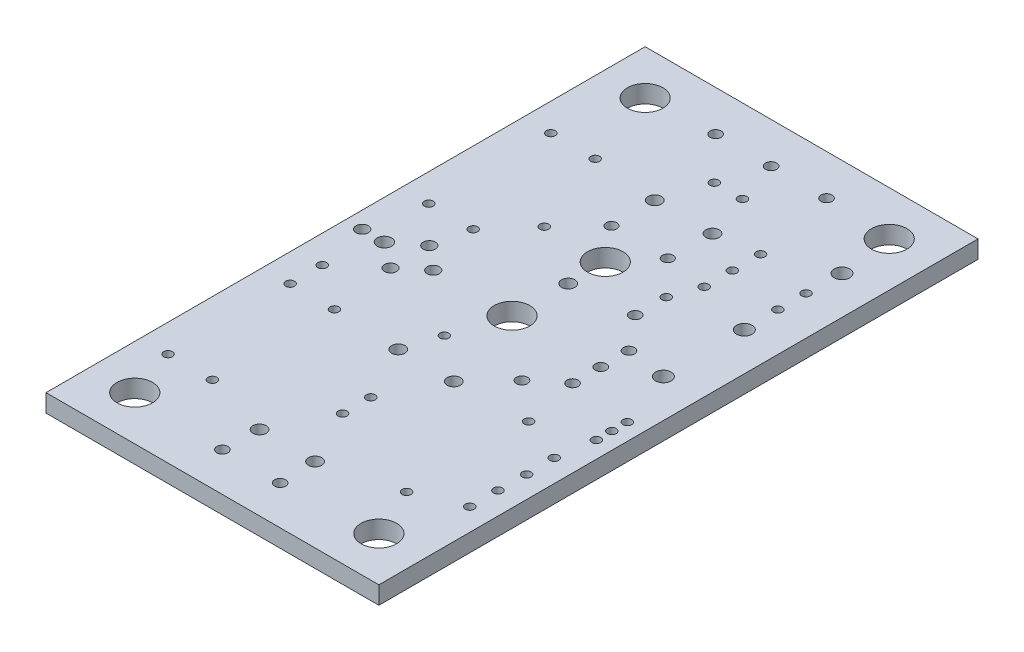
SolidWorks part; units mm, degrees
ref_plane "Plan de face" through (0, 0, 0) normal (0, 0, 1) x (1, 0, 0)
ref_plane "Plan de dessus" through (0, 0, 0) normal (0, 1, 0) x (1, 0, 0)
ref_plane "Plan de droite" through (0, 0, 0) normal (1, 0, 0) x (0, 0, -1)
sketch "Esquisse2" plane through (0, 0, 0) normal (0, 1, 0) x (1, 0, 0)
  line L0 (-3.7147, 54) -> (37.2981, 54) construction
  line L1 (0, 0) -> (30, 0)
  line L2 (0, 0) -> (0, 54)
  line L3 (0, 54) -> (30, 54)
  line L4 (30, 0) -> (30, 54)
  line L5 (30, 56.5565) -> (30, 31.4196) construction
  line L6 (21.4, 56.5565) -> (21.4, 32.6009) construction
  line L7 (39.5472, 43) -> (18.8423, 43) construction
  line L8 (22.2978, 35.4025) -> (8.7432, 35.4025) construction
  line L9 (9.5, 39.4589) -> (9.5, 30.7618) construction
  line L10 (0, 55.1911) -> (0, 37.1099) construction
  line L11 (20.5, 33.9139) -> (20.5, 38.4988) construction
  circle A0 centre (17.6225, 42.4459) radius 0.5994
  circle A1 centre (12.4206, 42.4459) radius 0.5994
  circle A2 centre (15.0216, 32.0446) radius 0.5994
  circle A3 centre (15.0038, 35.4025) radius 1.6002
  circle A4 centre (17.5997, 3.5001) radius 0.5004
  circle A5 centre (12.4003, 3.5001) radius 0.5004
  circle A6 centre (15.0012, 50.3504) radius 0.5004
  circle A7 centre (20, 50.3504) radius 0.5004
  circle A8 centre (10, 50.3504) radius 0.5004
  circle A9 centre (12.4993, 19.2507) radius 0.5994
  circle A10 centre (12.4993, 6.7488) radius 0.5994
  circle A11 centre (17.5006, 19.2507) radius 0.5994
  circle A12 centre (17.5006, 6.7488) radius 0.5994
  circle A13 centre (20.5003, 22.4003) radius 0.5004
  circle A14 centre (20.5003, 32.6009) radius 0.5004
  circle A15 centre (12.4612, 38.4988) radius 0.4826
  circle A16 centre (17.5412, 38.4988) radius 0.4826
  circle A17 centre (16.2712, 46.4998) radius 0.3988
  circle A18 centre (13.7312, 46.4998) radius 0.3988
  circle A19 centre (15.0012, 11.7297) radius 0.3988
  circle A20 centre (15.0012, 14.2697) radius 0.3988
  circle A21 centre (1.4986, 27.0002) radius 0.5512
  circle A22 centre (7.8994, 27.0002) radius 0.5512
  circle A23 centre (5.7988, 25.2501) radius 0.5512
  circle A24 centre (5.7988, 28.7503) radius 0.5512
  circle A25 centre (3.5001, 27.0002) radius 0.6502
  circle A26 centre (4.0005, 49.9999) radius 1.6002
  circle A27 centre (25.9994, 49.9999) radius 1.6002
  circle A28 centre (4.0005, 4.0005) radius 1.6002
  circle A29 centre (15.0012, 27.0002) radius 1.6002
  circle A30 centre (25.9994, 4.0005) radius 1.6002
  circle A31 centre (22.9997, 24.4602) radius 0.5004
  circle A32 centre (22.9997, 27.0002) radius 0.5004
  circle A33 centre (22.9997, 29.5402) radius 0.5004
  circle A34 centre (28.0492, 15.2705) radius 0.3988
  circle A35 centre (28.001, 12.7305) radius 0.3988
  circle A36 centre (28.001, 10.1905) radius 0.3988
  circle A37 centre (28.001, 17.8105) radius 0.3988
  circle A38 centre (26.4998, 41.9989) radius 0.3988
  circle A39 centre (26.4998, 39.4589) radius 0.3988
  circle A40 centre (26.5608, 45.179) radius 0.701
  circle A41 centre (26.5608, 36.3804) radius 0.701
  circle A42 centre (26.5608, 29.0805) radius 0.701
  circle A43 centre (24.0005, 8.4988) radius 0.3988
  circle A44 centre (24.0005, 19.4996) radius 0.3988
  circle A45 centre (6.4999, 42.9997) radius 0.3988
  circle A46 centre (6.4999, 31.9989) radius 0.3988
  circle A47 centre (2.4994, 42.9997) radius 0.3988
  circle A48 centre (2.4994, 31.9989) radius 0.3988
  circle A49 centre (6.4999, 8.4988) radius 0.3988
  circle A50 centre (6.4999, 19.4996) radius 0.3988
  circle A51 centre (2.4994, 8.4988) radius 0.3988
  circle A52 centre (2.4994, 19.4996) radius 0.3988
  circle A53 centre (2.4994, 22.4003) radius 0.3988
  circle A54 centre (13.5001, 22.4003) radius 0.3988
  circle A55 centre (28.4988, 21.0998) radius 0.3988
  circle A56 centre (28.4988, 22.4993) radius 0.3988
  circle A57 centre (28.4988, 23.8989) radius 0.3988
  circle A58 centre (21.4, 43) radius 0.4
  circle A59 centre (21.4, 40.46) radius 0.4
  circle A60 centre (21.4, 37.92) radius 0.4
  circle A61 centre (20.5, 35.4025) radius 0.4
  circle A62 centre (9.5, 35.4025) radius 0.4
  dimension "D3" = 9.5
  dimension "D1" = 8.6
  dimension "D2" = 11
  dimension "D4" = 11
extrude "Extrusion1" add sketch "Esquisse2" along normal blind 1.6
